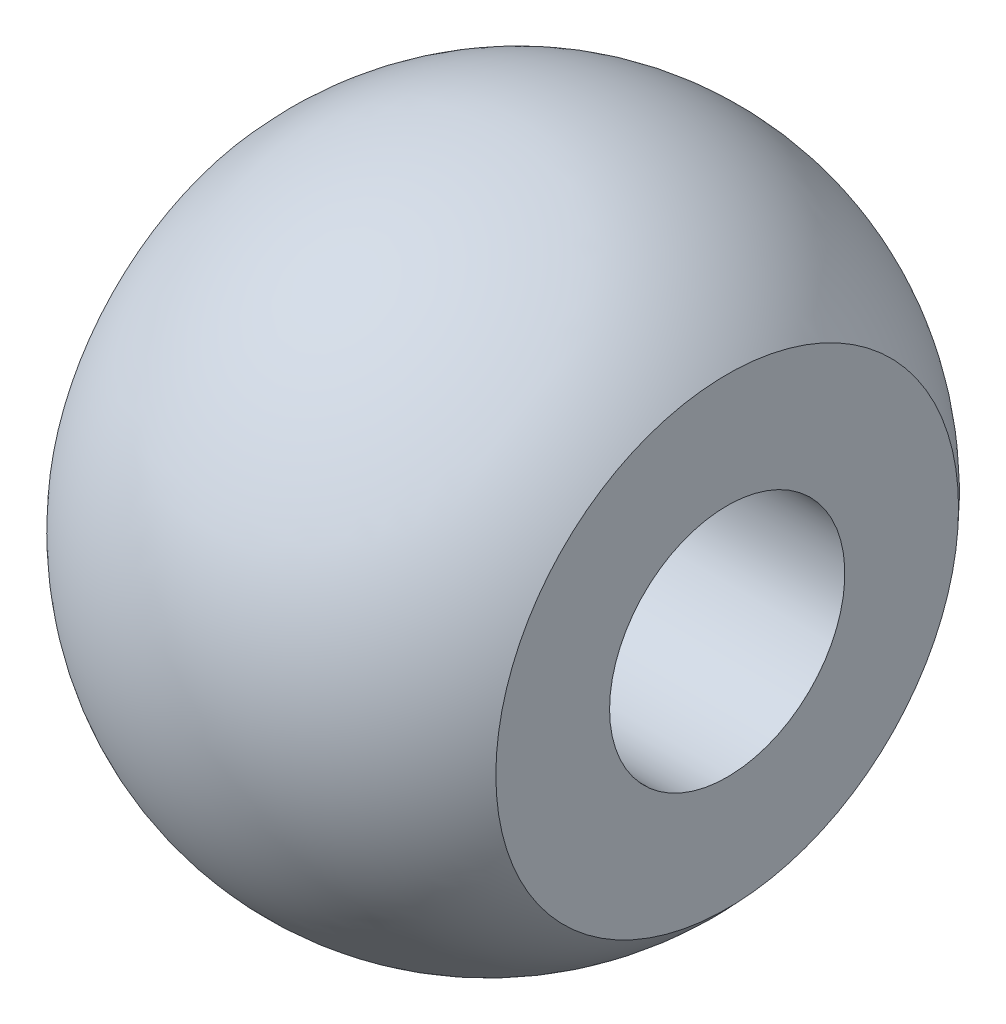
SolidWorks part; units mm, degrees
ref_plane "Front Plane" through (0, 0, 0) normal (0, 0, 1) x (1, 0, 0)
ref_plane "Top Plane" through (0, 0, 0) normal (0, 1, 0) x (1, 0, 0)
ref_plane "Right Plane" through (0, 0, 0) normal (1, 0, 0) x (0, 0, -1)
sketch "Sketch1" plane through (0, 0, 0) normal (0, 0, 1) x (1, 0, 0)
  line L0 (-2.8025, 0) -> (6.5391, 0) construction
  line L1 (-2.0879, 2.3613) -> (5.9121, 2.3613)
  line L2 (5.9121, 2.3613) -> (5.9121, 4.6448)
  line L3 (-2.0879, 2.3613) -> (-3.0879, 3.1658)
  line L4 (-3.0879, 3.1658) -> (-3.0879, 4.6448)
  arc A0 (-3.0879, 4.6448) -> (5.9121, 4.6448) centre (1.4121, 0.6762) cw
  dimension "D1" = 6
  dimension "D2" = 1
  dimension "D3" = 9
revolve "Revolve1" add sketch "Sketch1" angle 360 about L0
